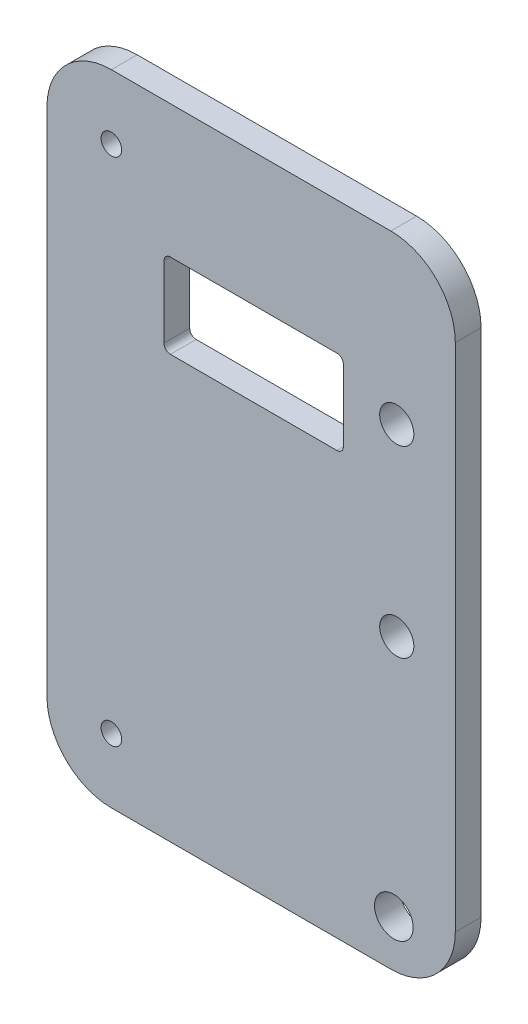
SolidWorks part; units mm, degrees
ref_plane "Front Plane" through (0, 0, 0) normal (0, 0, 1) x (1, 0, 0)
ref_plane "Top Plane" through (0, 0, 0) normal (0, 1, 0) x (1, 0, 0)
ref_plane "Right Plane" through (0, 0, 0) normal (1, 0, 0) x (0, 0, -1)
sketch "Sketch1" plane through (0, 0, 0) normal (0, 0, 1) x (1, 0, 0)
  line L1 (-108.4636, -267.8694) -> (-45.0794, -267.8694)
  line L2 (-108.4636, -267.8694) -> (-108.4636, -367.109)
  line L3 (-108.4636, -367.109) -> (-45.0794, -367.109)
  line L4 (-45.0794, -267.8694) -> (-45.0794, -367.109)
  line L5 (-63.4534, -301.5579) -> (-89.2971, -301.5579)
  line L6 (-62.4534, -300.5579) -> (-62.4534, -289.4797)
  line L7 (-63.4534, -288.4797) -> (-89.2971, -288.4797)
  line L8 (-90.2971, -300.5579) -> (-90.2971, -289.4797)
  arc A0 (-89.2971, -301.5579) -> (-90.2971, -300.5579) centre (-89.2971, -300.5579) cw
  arc A1 (-89.2971, -288.4797) -> (-90.2971, -289.4797) centre (-89.2971, -289.4797) ccw
  arc A2 (-62.4534, -289.4797) -> (-63.4534, -288.4797) centre (-63.4534, -289.4797) ccw
  arc A3 (-63.4534, -301.5579) -> (-62.4534, -300.5579) centre (-63.4534, -300.5579) ccw
  dimension "D1" = 1
extrude "Boss-Extrude1" add sketch "Sketch1" along normal blind 4
hole_wizard "M5 Clearance Hole1" positions "Sketch4" profile "Sketch2" hole size "M5" standard "ISO" end condition through all
sketch "Sketch4" plane through (0, 0, 4) normal (0, 0, 1) x (1, 0, 0)
  point P0 (-54.1627, -321.9157)
  point P2 (-54.1627, -293.4157)
sketch "Sketch2" plane through (-54.1627, -321.9157, 4) normal (1, 0, 0) x (0, -1, 0)
  line L0 (0, 0) -> (0, 4)
  line L1 (0, 4) -> (2.65, 4)
  line L2 (2.65, 4) -> (2.65, 0)
  line L5 (2.65, 0) -> (0, 0)
  line L11 (0, -6.35) -> (0, 107.95) construction
  dimension "Thru Hole Dia." = 5.3
  dimension "Thru Hole Depth" = 4
fillet "Fillet1" radius 10 4 edges at (-108.4636, -267.8694, 2) (-45.0794, -267.8694, 2) (-108.4636, -367.109, 2) (-45.0794, -367.109, 2)
hole_wizard "M5 Clearance Hole2" positions "Sketch6" profile "Sketch5" hole size "M5" standard "ISO" end condition through all
sketch "Sketch6" plane through (0, 0, 0) normal (0, 0, -1) x (-1, 0, 0)
  line L24 (-96.2636, -309.6657) -> (-96.2636, -364.3029) construction
  line L25 (-92.2636, -368.3029) -> (59.1173, -368.3029) construction
  line L26 (63.1173, -364.3029) -> (63.1173, -309.6657) construction
  line L27 (59.1173, -305.6657) -> (55.1173, -305.6657) construction
  line L28 (51.1173, -301.6657) -> (51.1173, -289.4157) construction
  line L29 (47.1173, -285.4157) -> (-80.2636, -285.4157) construction
  line L30 (-84.2636, -289.4157) -> (-84.2636, -301.6657) construction
  line L31 (-88.2636, -305.6657) -> (-92.2636, -305.6657) construction
  arc A24 (-96.2636, -364.3029) -> (-92.2636, -368.3029) centre (-92.2636, -364.3029) ccw construction
  arc A25 (59.1173, -368.3029) -> (63.1173, -364.3029) centre (59.1173, -364.3029) ccw construction
  arc A26 (63.1173, -309.6657) -> (59.1173, -305.6657) centre (59.1173, -309.6657) ccw construction
  arc A27 (51.1173, -301.6657) -> (55.1173, -305.6657) centre (55.1173, -301.6657) ccw construction
  arc A28 (51.1173, -289.4157) -> (47.1173, -285.4157) centre (47.1173, -289.4157) ccw construction
  arc A29 (-80.2636, -285.4157) -> (-84.2636, -289.4157) centre (-80.2636, -289.4157) ccw construction
  arc A30 (-88.2636, -305.6657) -> (-84.2636, -301.6657) centre (-88.2636, -301.6657) ccw construction
  arc A31 (-92.2636, -305.6657) -> (-96.2636, -309.6657) centre (-92.2636, -309.6657) ccw construction
  point P0 (54.6173, -359.8029)
  dimension "D1" = 8.5
  dimension "D2" = 8.5
sketch "Sketch5" plane through (-54.6173, -359.8029, 0) normal (1, 0, 0) x (0, 1, 0)
  line L0 (0, 0) -> (0, 4)
  line L1 (0, 4) -> (3, 4)
  line L2 (3, 4) -> (3, 0)
  line L5 (3, 0) -> (0, 0)
  line L11 (0, -6.35) -> (0, 107.95) construction
  dimension "Thru Hole Dia." = 6
  dimension "Thru Hole Depth" = 4
sketch "Sketch7" plane through (0, 0, 4) normal (0, 0, 1) x (1, 0, 0)
  line L0 (-108.4636, -277.8694) -> (-108.4636, -357.109) construction
  line L1 (-108.4636, -333.6557) -> (-105.4252, -333.6557)
  line L2 (-108.4636, -333.6557) -> (-108.4636, -305.6397)
  line L3 (-79.3727, -256.1535) -> (-105.4252, -256.1535)
  line L4 (-105.4252, -333.6557) -> (-105.4252, -256.1535)
  line L7 (-108.4636, -305.6397) -> (-79.3727, -305.6397)
  line L8 (-79.3727, -256.1535) -> (-79.3727, -305.6397)
extrude "Boss-Extrude2" [suppressed] add sketch "Sketch7" against normal up to surface (4 mm away)
sketch "Sketch8" [suppressed] plane through (0, 0, 0) normal (0, 0, -1) x (-1, 0, 0)
  line L0 (79.3727, -305.6397) -> (63.2759, -305.6397) construction
  line L1 (71.3243, -251.637) -> (23.8623, -251.637)
  line L2 (71.3243, -251.637) -> (71.3243, -305.6397)
  line L3 (71.3243, -305.6397) -> (23.8623, -305.6397)
  line L4 (23.8623, -251.637) -> (23.8623, -305.6397)
extrude "Cut-Extrude1" [suppressed] cut sketch "Sketch8" against normal blind 14.4
fillet "Fillet2" [suppressed] radius 8
hole_wizard "M3 Clearance Hole1" positions "Sketch10" profile "Sketch9" hole size "M3" standard "ISO" end condition through all
sketch "Sketch10" plane through (0, 0, 4) normal (0, 0, 1) x (1, 0, 0)
  point P0 (-98.4636, -357.109)
  point P3 (-98.4636, -277.8694)
sketch "Sketch9" plane through (-98.4636, -357.109, 4) normal (1, 0, 0) x (0, -1, 0)
  line L0 (0, 0) -> (0, 4)
  line L1 (0, 4) -> (1.6, 4)
  line L2 (1.6, 4) -> (1.6, 0)
  line L5 (1.6, 0) -> (0, 0)
  line L11 (0, -6.35) -> (0, 107.95) construction
  dimension "Thru Hole Dia." = 3.2
  dimension "Thru Hole Depth" = 4
